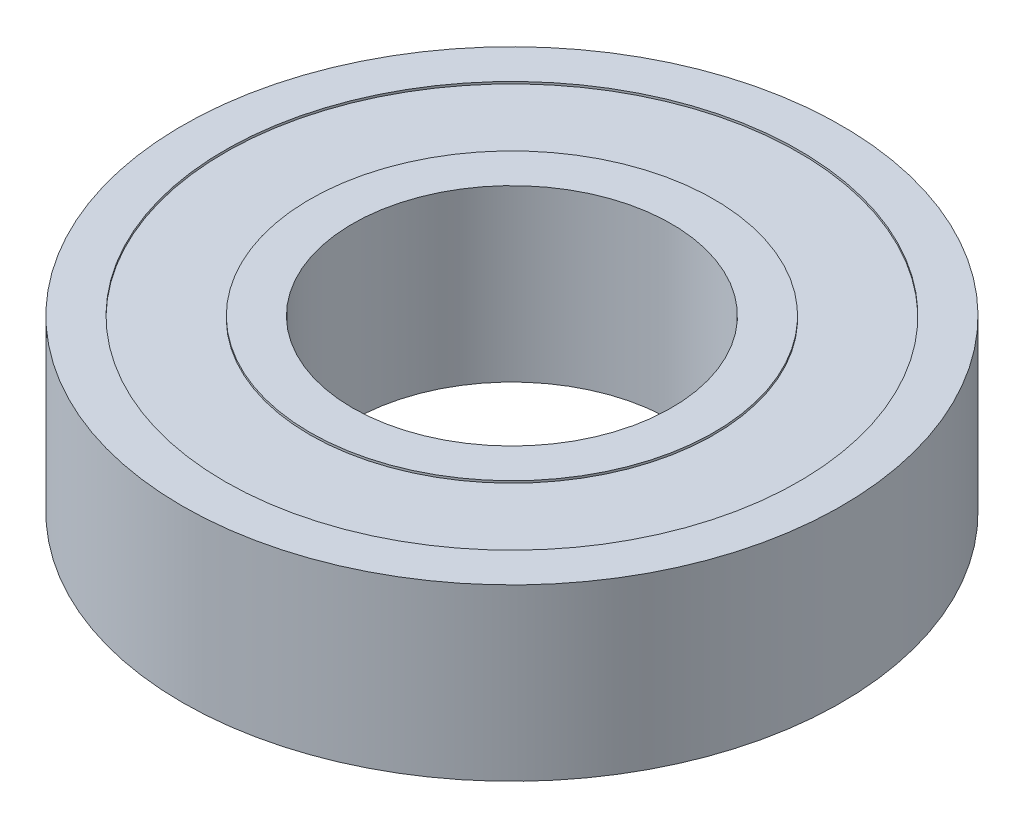
SolidWorks part; units mm, degrees
ref_plane "Přední rovina" through (0, 0, 0) normal (0, 0, 1) x (1, 0, 0)
ref_plane "Horní rovina" through (0, 0, 0) normal (0, 1, 0) x (1, 0, 0)
ref_plane "Pravá rovina" through (0, 0, 0) normal (1, 0, 0) x (0, 0, -1)
sketch "Skica1" plane through (0, 0, 0) normal (0, 0, 1) x (1, 0, 0)
  line L0 (0, 16.0849) -> (0, -10.0638) construction
  line L1 (31, 0) -> (31, 16)
  line L2 (31, 16) -> (27, 16)
  line L3 (27, 16) -> (27, 15.8)
  line L4 (27, 15.8) -> (19, 15.8)
  line L5 (19, 15.8) -> (19, 16)
  line L6 (19, 16) -> (15, 16)
  line L7 (15, 16) -> (15, 0)
  line L8 (15, 0) -> (19, 0)
  line L9 (19, 0) -> (19, 0.2)
  line L10 (19, 0.2) -> (27, 0.2)
  line L11 (27, 0.2) -> (27, 0)
  line L12 (27, 0) -> (31, 0)
  point P5 (24.5522, 0)
  point P16 (27, 1.0762)
  dimension "D1" = 30
  dimension "D2" = 62
  dimension "D3" = 4
  dimension "D4" = 4
  dimension "D5" = 0.2
  dimension "D6" = 16
revolve "Rotovat1" add sketch "Skica1" angle 360 about L0
